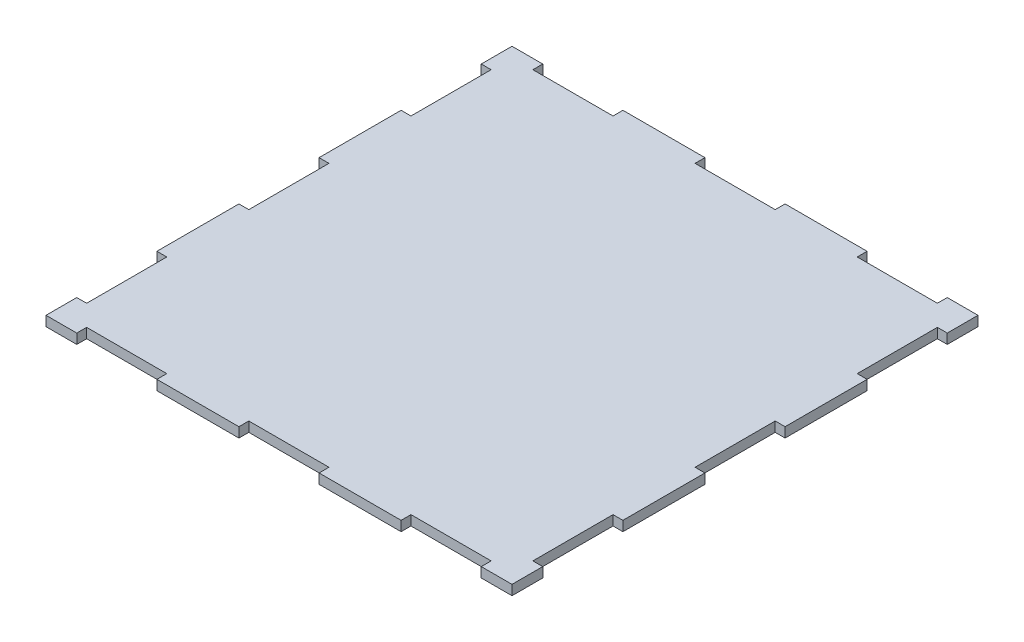
SolidWorks part; units mm, degrees
ref_plane "Front Plane" through (0, 0, 0) normal (0, 0, 1) x (1, 0, 0)
ref_plane "Top Plane" through (0, 0, 0) normal (0, 1, 0) x (1, 0, 0)
ref_plane "Right Plane" through (0, 0, 0) normal (1, 0, 0) x (0, 0, -1)
sketch "Sketch1" plane through (0, 0, 0) normal (0, 1, 0) x (1, 0, 0)
  line L1 (75, -75) -> (-75, -75)
  line L2 (75, -75) -> (75, 75)
  line L3 (75, 75) -> (-75, 75)
  line L4 (-75, -75) -> (-75, 75)
  line L5 (75, -75) -> (-75, 75) construction
  line L6 (75, 75) -> (-75, -75) construction
  point P0 (0, 0)
  dimension "D1" = 150
  dimension "D2" = 150
extrude "Boss-Extrude1" add sketch "Sketch1" along normal blind 3.18
sketch "Sketch6" plane through (0, 0, 0) normal (0, -1, 0) x (1, 0, 0)
  line L0 (-75, 75) -> (75, 75) construction
  line L1 (0, 75) -> (-12.9, 75)
  line L2 (0, 75) -> (0, 71.82)
  line L3 (0, 71.82) -> (-12.9, 71.82)
  line L4 (-12.9, 75) -> (-12.9, 71.82)
  line L5 (-75, -75) -> (-75, 75) construction
  line L6 (-65.1, 75) -> (-39.3, 75)
  line L7 (-65.1, 75) -> (-65.1, 71.82)
  line L8 (-65.1, 71.82) -> (-39.3, 71.82)
  line L9 (-39.3, 75) -> (-39.3, 71.82)
  point P10 (-65.1, 73.41)
  dimension "D1" = 12.9
  dimension "D2" = 3.18
  dimension "D3" = 25.8
  dimension "D4" = 3.18
  dimension "D5" = 9.9
extrude "Cut-Extrude1" cut sketch "Sketch6" against normal blind 10
mirror "Mirror1" about plane through (0, 0, 0) normal (1, 0, 0) of "Cut-Extrude1"
mirror "Mirror2" about plane through (0, 0, 0) normal (0, 0, 1) of "Mirror1", "Cut-Extrude1"
ref_plane "Plane10" through (0, 0, 0) normal (0.7071, 0, 0.7071) x (0.7071, 0, -0.7071)
mirror "Mirror3" about plane through (0, 0, 0) normal (0.7071, 0, 0.7071) of "Mirror1", "Cut-Extrude1"
mirror "Mirror4" about plane through (0, 0, 0) normal (1, 0, 0) of "Mirror3"
sketch "Sketch8" [suppressed] plane through (0, 3.18, 0) normal (0, 1, 0) x (1, 0, 0)
  line L0 (0, 0) -> (0, -92.6186) construction
  line L1 (-39.3, -75) -> (-12.9, -75) construction
  circle A0 centre (-16.5, -35) radius 1.6
  dimension "D1" = 3.2
  dimension "D2" = 16.5
  dimension "D3" = 40
extrude "Cut-Extrude3" [suppressed] cut sketch "Sketch8" against normal blind 10
mirror "Mirror5" [suppressed] about plane through (0, 0, 0) normal (1, 0, 0)
sketch "Sketch9" [suppressed] plane through (0, 3.18, 0) normal (0, 1, 0) x (1, 0, 0)
  line L0 (-39.3, -75) -> (-12.9, -75) construction
  circle A0 centre (-11.5, -35) radius 1.6
  circle A1 centre (-16.5, -35) radius 1.6 construction
  dimension "D1" = 3.2
  dimension "D2" = 5
  dimension "D3" = 40
extrude "Cut-Extrude4" [suppressed] cut sketch "Sketch9" against normal blind 10
mirror "Mirror6" [suppressed] about plane through (0, 0, 0) normal (1, 0, 0)
sketch "Sketch10" [suppressed] plane through (0, 3.18, 0) normal (0, 1, 0) x (1, 0, 0)
  line L0 (0, 0) -> (0, -92.1497) construction
  line L1 (12.9, -71.82) -> (-12.9, -71.82) construction
  line L2 (-10, -17.82) -> (10, -17.82)
  line L3 (-10, -17.82) -> (-10, -21.82)
  line L4 (-10, -21.82) -> (10, -21.82)
  line L5 (10, -17.82) -> (10, -21.82)
  line L6 (-10, -17.82) -> (10, -21.82) construction
  line L7 (-10, -21.82) -> (10, -17.82) construction
  point P3 (0, -19.82)
  dimension "D1" = 4
  dimension "D2" = 20
  dimension "D3" = 50
extrude "Cut-Extrude5" [suppressed] cut sketch "Sketch10" against normal blind 10
